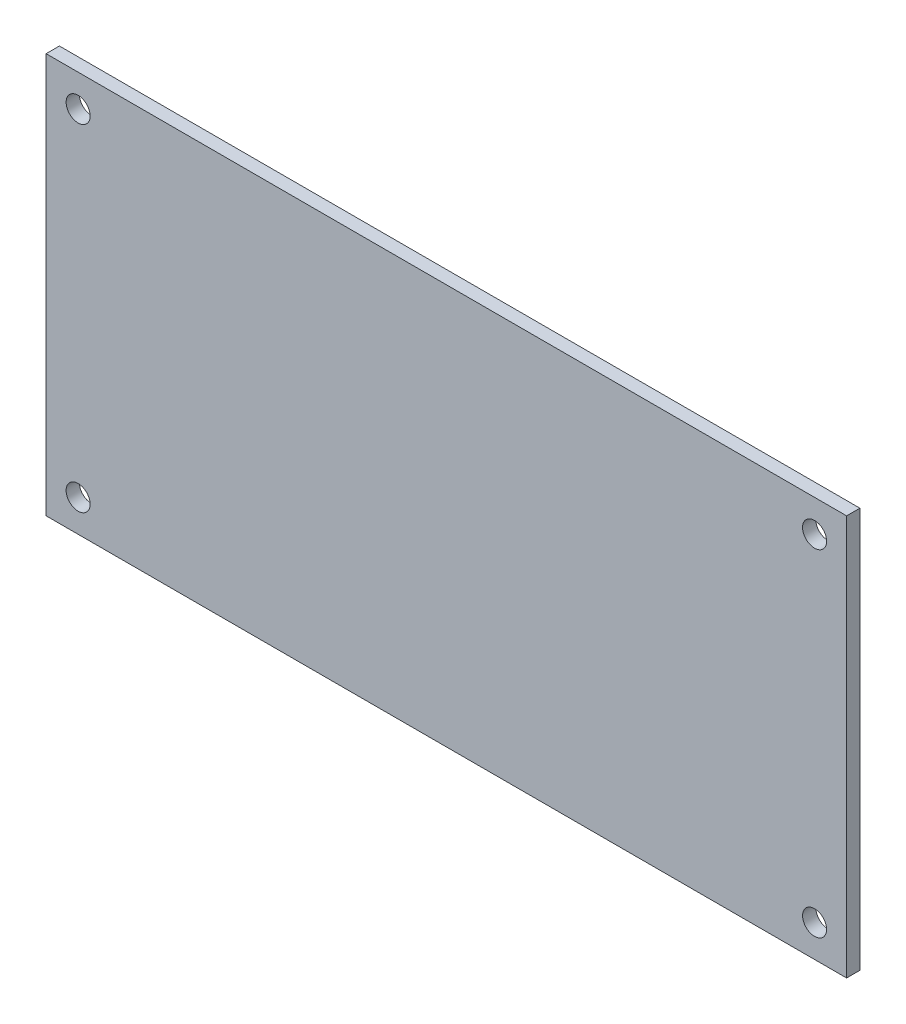
SolidWorks part; units mm, degrees
material "Epoxy, renforcé"
ref_plane "Plan de face" through (0, 0, 0) normal (0, 0, 1) x (1, 0, 0)
ref_plane "Plan de dessus" through (0, 0, 0) normal (0, 1, 0) x (1, 0, 0)
ref_plane "Plan de droite" through (0, 0, 0) normal (1, 0, 0) x (0, 0, -1)
sketch "Esquisse1" plane through (0, 0, 0) normal (0, 0, 1) x (1, 0, 0)
  line L1 (50, 25) -> (-50, 25)
  line L2 (50, 25) -> (50, -25)
  line L3 (50, -25) -> (-50, -25)
  line L4 (-50, 25) -> (-50, -25)
  line L5 (50, 25) -> (-50, -25) construction
  line L6 (50, -25) -> (-50, 25) construction
  line L7 (46, 21) -> (-46, 21) construction
  line L8 (46, 21) -> (46, -21) construction
  line L9 (46, -21) -> (-46, -21) construction
  line L10 (-46, 21) -> (-46, -21) construction
  line L11 (46, 21) -> (-46, -21) construction
  line L12 (46, -21) -> (-46, 21) construction
  circle A0 centre (-46, 21) radius 1.5
  circle A1 centre (-46, -21) radius 1.5
  circle A2 centre (46, 21) radius 1.5
  circle A3 centre (46, -21) radius 1.5
  point P0 (0, 0)
  point P6 (0, 0)
  dimension "D5" = 3
  dimension "D6" = 3
  dimension "D7" = 3
  dimension "D8" = 3
  dimension "D1" = 50
  dimension "D2" = 100
  dimension "D3" = 4
  dimension "D4" = 4
  dimension "D9" = 4
extrude "Boss.-Extru.1" add sketch "Esquisse1" along normal blind 1.66
